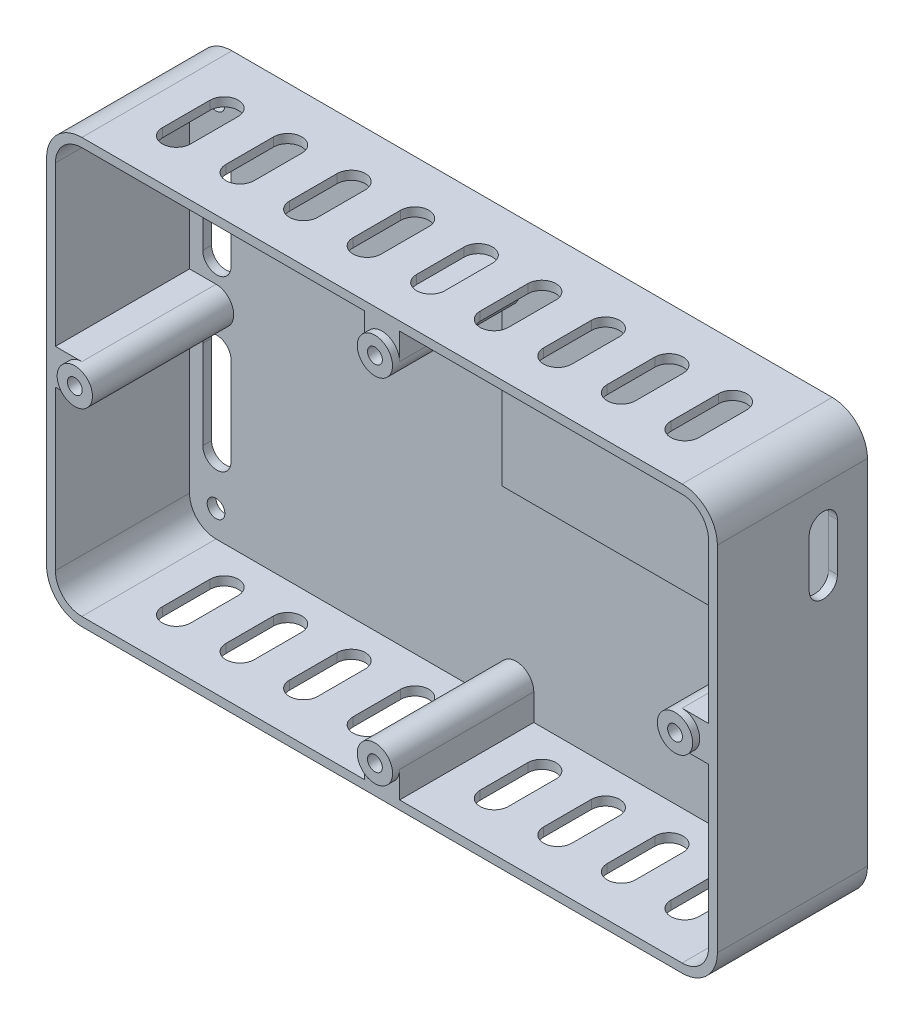
SolidWorks part; units mm, degrees
ref_plane "Front Plane" through (0, 0, 0) normal (0, 0, 1) x (1, 0, 0)
ref_plane "Top Plane" through (0, 0, 0) normal (0, 1, 0) x (1, 0, 0)
ref_plane "Right Plane" through (0, 0, 0) normal (1, 0, 0) x (0, 0, -1)
sketch "Sketch1" plane through (0, 0, 0) normal (0, 0, 1) x (1, 0, 0)
  line L0 (92.3241, -194.8914) -> (92.3241, -94.8914) construction
  line L1 (-85.1759, -202.3914) -> (84.8241, -202.3914) construction
  line L2 (84.8241, -87.3914) -> (-85.1759, -87.3914) construction
  line L3 (-92.6759, -94.8914) -> (-92.6759, -194.8914) construction
  line L4 (-85.1759, -204.8914) -> (84.8241, -204.8914)
  line L5 (94.8241, -194.8914) -> (94.8241, -94.8914)
  line L6 (84.8241, -84.8914) -> (-85.1759, -84.8914)
  line L7 (-95.1759, -94.8914) -> (-95.1759, -194.8914)
  line L8 (-85.1759, -204.8914) -> (84.8241, -204.8914)
  line L9 (94.8241, -194.8914) -> (94.8241, -94.8914)
  line L10 (84.8241, -84.8914) -> (-85.1759, -84.8914)
  line L11 (-95.1759, -94.8914) -> (-95.1759, -194.8914)
  line L12 (92.3241, -194.8914) -> (92.3241, -94.8914)
  line L13 (-85.1759, -202.3914) -> (84.8241, -202.3914)
  line L14 (84.8241, -87.3914) -> (-85.1759, -87.3914)
  line L15 (-92.6759, -94.8914) -> (-92.6759, -194.8914)
  line L16 (-85.1759, -87.3914) -> (-85.1759, -87.2984)
  circle A0 centre (-85.1759, -94.8914) radius 5.5
  circle A1 centre (84.8241, -94.8914) radius 5.9759
  circle A2 centre (84.8241, -194.8914) radius 5.9759
  circle A3 centre (-85.1759, -194.8914) radius 5.9759
  arc A4 (84.8241, -204.8914) -> (94.8241, -194.8914) centre (84.8241, -194.8914) ccw
  arc A5 (94.8241, -94.8914) -> (84.8241, -84.8914) centre (84.8241, -94.8914) ccw
  arc A6 (-85.1759, -84.8914) -> (-95.1759, -94.8914) centre (-85.1759, -94.8914) ccw
  arc A7 (-95.1759, -194.8914) -> (-85.1759, -204.8914) centre (-85.1759, -194.8914) ccw
  arc A8 (84.8241, -204.8914) -> (94.8241, -194.8914) centre (84.8241, -194.8914) ccw
  arc A9 (94.8241, -94.8914) -> (84.8241, -84.8914) centre (84.8241, -94.8914) ccw
  arc A10 (-85.1759, -84.8914) -> (-95.1759, -94.8914) centre (-85.1759, -94.8914) ccw
  arc A11 (-95.1759, -194.8914) -> (-85.1759, -204.8914) centre (-85.1759, -194.8914) ccw
  circle A13 centre (-85.1759, -194.8914) radius 7.5
  circle A14 centre (84.8241, -94.8914) radius 7.5
  circle A15 centre (84.8241, -194.8914) radius 7.5
  arc A16 (-92.6759, -94.8914) -> (-85.1759, -87.3914) centre (-85.1759, -94.8914) ccw
  dimension "D2" = 11
  dimension "D1" = 0
extrude "Boss-Extrude1" add sketch "Sketch1" along normal blind 2
sketch "Sketch2" plane through (0, 0, 2) normal (0, 0, 1) x (1, 0, 0)
  line L4 (-95.1759, -94.8914) -> (-95.1759, -194.8914)
  line L5 (-85.1759, -204.8914) -> (84.8241, -204.8914)
  line L6 (94.8241, -194.8914) -> (94.8241, -94.8914)
  line L7 (84.8241, -84.8914) -> (-85.1759, -84.8914)
  line L8 (-95.1759, -94.8914) -> (-95.1759, -194.8914)
  line L9 (-85.1759, -204.8914) -> (84.8241, -204.8914)
  line L10 (94.8241, -194.8914) -> (94.8241, -94.8914)
  line L11 (84.8241, -84.8914) -> (-85.1759, -84.8914)
  arc A4 (-95.1759, -194.8914) -> (-85.1759, -204.8914) centre (-85.1759, -194.8914) ccw
  arc A5 (84.8241, -204.8914) -> (94.8241, -194.8914) centre (84.8241, -194.8914) ccw
  arc A6 (94.8241, -94.8914) -> (84.8241, -84.8914) centre (84.8241, -94.8914) ccw
  arc A7 (-85.1759, -84.8914) -> (-95.1759, -94.8914) centre (-85.1759, -94.8914) ccw
  arc A8 (-95.1759, -194.8914) -> (-85.1759, -204.8914) centre (-85.1759, -194.8914) ccw
  arc A9 (84.8241, -204.8914) -> (94.8241, -194.8914) centre (84.8241, -194.8914) ccw
  arc A10 (94.8241, -94.8914) -> (84.8241, -84.8914) centre (84.8241, -94.8914) ccw
  arc A11 (-85.1759, -84.8914) -> (-95.1759, -94.8914) centre (-85.1759, -94.8914) ccw
  dimension "D1" = 0
extrude "Boss-Extrude2" add sketch "Sketch2" along normal blind 2.5
sketch "Sketch3" plane through (0, 0, 4.5) normal (0, 0, 1) x (1, 0, 0)
  line L0 (-85.1759, -94.8914) -> (84.8241, -94.8914) construction
  line L1 (84.8241, -94.8914) -> (84.8241, -194.8914) construction
  line L2 (84.8241, -194.8914) -> (-85.1759, -194.8914) construction
  line L3 (-85.1759, -194.8914) -> (-85.1759, -94.8914) construction
  line L8 (-85.1759, -204.8914) -> (84.8241, -204.8914) construction
  line L9 (94.8241, -194.8914) -> (94.8241, -94.8914) construction
  line L10 (84.8241, -84.8914) -> (-85.1759, -84.8914) construction
  line L11 (-95.1759, -94.8914) -> (-95.1759, -194.8914) construction
  line L12 (-92.6759, -94.8914) -> (-92.6759, -194.8914)
  line L13 (-85.1759, -202.3914) -> (84.8241, -202.3914)
  line L14 (92.3241, -194.8914) -> (92.3241, -94.8914)
  line L15 (84.8241, -87.3914) -> (-85.1759, -87.3914)
  line L16 (-92.6759, -94.8914) -> (-92.6759, -194.8914)
  line L17 (-85.1759, -202.3914) -> (84.8241, -202.3914)
  line L18 (92.3241, -194.8914) -> (92.3241, -94.8914)
  line L19 (84.8241, -87.3914) -> (-85.1759, -87.3914)
  line L20 (-85.1759, -204.8914) -> (84.8241, -204.8914)
  line L21 (94.8241, -194.8914) -> (94.8241, -94.8914)
  line L22 (84.8241, -84.8914) -> (-85.1759, -84.8914)
  line L23 (-95.1759, -94.8914) -> (-95.1759, -194.8914)
  line L24 (-85.1759, -139.8914) -> (-92.6759, -139.8914)
  line L25 (-85.1759, -149.8914) -> (-92.6759, -149.8914)
  line L26 (-5.1759, -94.8914) -> (-5.1759, -87.3914)
  line L27 (4.8241, -94.8914) -> (4.8241, -87.3914)
  line L28 (-5.1759, -194.8914) -> (-5.1759, -202.3914)
  line L29 (4.8241, -194.8914) -> (4.8241, -202.3914)
  line L30 (84.8241, -139.8914) -> (92.3241, -139.8914)
  line L33 (84.8241, -149.8914) -> (92.3241, -149.8914)
  circle A0 centre (-0.1759, -94.8914) radius 5
  circle A1 centre (-85.1759, -144.8914) radius 5
  circle A2 centre (-0.1759, -194.8914) radius 5
  circle A3 centre (84.8241, -144.8914) radius 5
  arc A8 (-95.1759, -194.8914) -> (-85.1759, -204.8914) centre (-85.1759, -194.8914) ccw construction
  arc A9 (84.8241, -204.8914) -> (94.8241, -194.8914) centre (84.8241, -194.8914) ccw construction
  arc A10 (94.8241, -94.8914) -> (84.8241, -84.8914) centre (84.8241, -94.8914) ccw construction
  arc A11 (-85.1759, -84.8914) -> (-95.1759, -94.8914) centre (-85.1759, -94.8914) ccw construction
  arc A12 (-85.1759, -87.3914) -> (-92.6759, -94.8914) centre (-85.1759, -94.8914) ccw
  arc A13 (-92.6759, -194.8914) -> (-85.1759, -202.3914) centre (-85.1759, -194.8914) ccw
  arc A14 (84.8241, -202.3914) -> (92.3241, -194.8914) centre (84.8241, -194.8914) ccw
  arc A15 (92.3241, -94.8914) -> (84.8241, -87.3914) centre (84.8241, -94.8914) ccw
  arc A16 (-85.1759, -87.3914) -> (-92.6759, -94.8914) centre (-85.1759, -94.8914) ccw
  arc A17 (-92.6759, -194.8914) -> (-85.1759, -202.3914) centre (-85.1759, -194.8914) ccw
  arc A18 (84.8241, -202.3914) -> (92.3241, -194.8914) centre (84.8241, -194.8914) ccw
  arc A19 (92.3241, -94.8914) -> (84.8241, -87.3914) centre (84.8241, -94.8914) ccw
  arc A20 (-95.1759, -194.8914) -> (-85.1759, -204.8914) centre (-85.1759, -194.8914) ccw
  arc A21 (84.8241, -204.8914) -> (94.8241, -194.8914) centre (84.8241, -194.8914) ccw
  arc A22 (94.8241, -94.8914) -> (84.8241, -84.8914) centre (84.8241, -94.8914) ccw
  arc A23 (-85.1759, -84.8914) -> (-95.1759, -94.8914) centre (-85.1759, -94.8914) ccw
  arc M9 (-85.1759, -84.8914) -> (-95.1759, -94.8914) centre (-85.1759, -94.8914) ccw
  line M10 (-95.1759, -94.8914) -> (-95.1759, -194.8914)
  arc M11 (-95.1759, -194.8914) -> (-85.1759, -204.8914) centre (-85.1759, -194.8914) ccw
  line M12 (-85.1759, -204.8914) -> (84.8241, -204.8914)
  arc M13 (84.8241, -204.8914) -> (94.8241, -194.8914) centre (84.8241, -194.8914) ccw
  line M14 (94.8241, -194.8914) -> (94.8241, -94.8914)
  arc M15 (94.8241, -94.8914) -> (84.8241, -84.8914) centre (84.8241, -94.8914) ccw
  line M16 (84.8241, -84.8914) -> (-85.1759, -84.8914)
  dimension "D1" = 10
  dimension "D2" = 2.5
extrude "Boss-Extrude3" add sketch "Sketch3" along normal blind 38 contours A19 L18 A18 L17 A17 L16 A16 L19 M16 M9 M10 M11 M12 M13 M14 M15 | A0 L27 L19 L26 | A0 | A3 | A3 L33 L18 L30 | A2 | A2 L28 L17 L29 | A1 L24 L16 L25 | A1
sketch "Sketch5" plane through (0, 0, 42.5) normal (0, 0, 1) x (1, 0, 0)
  circle A0 centre (-85.1759, -144.8914) radius 5
  circle A1 centre (-0.1759, -94.8914) radius 5
  circle A2 centre (84.8241, -144.8914) radius 5
  circle A3 centre (-0.1759, -194.8914) radius 5
extrude "Boss-Extrude4" add sketch "Sketch5" along normal blind 2
sketch "Sketch6" plane through (0, 0, 4.5) normal (0, 0, 1) x (1, 0, 0)
  line L2 (-80.9375, -181.3615) -> (-80.9375, -156.298)
  line L3 (-88.9375, -156.298) -> (-88.9375, -181.3615)
  line L4 (-80.9375, -181.3615) -> (-80.9375, -156.298)
  line L5 (-88.9375, -156.298) -> (-88.9375, -181.3615)
  line L6 (-80.9375, -133.4848) -> (-80.9375, -108.4213)
  line L7 (-88.9375, -108.4213) -> (-88.9375, -133.4848)
  line L8 (-80.9375, -133.4848) -> (-80.9375, -108.4213)
  line L9 (-88.9375, -108.4213) -> (-88.9375, -133.4848)
  arc A2 (-80.9375, -156.298) -> (-88.9375, -156.298) centre (-84.9375, -156.298) ccw
  arc A3 (-88.9375, -181.3615) -> (-80.9375, -181.3615) centre (-84.9375, -181.3615) ccw
  arc A4 (-80.9375, -156.298) -> (-88.9375, -156.298) centre (-84.9375, -156.298) ccw
  arc A5 (-88.9375, -181.3615) -> (-80.9375, -181.3615) centre (-84.9375, -181.3615) ccw
  arc A6 (-88.9375, -133.4848) -> (-80.9375, -133.4848) centre (-84.9375, -133.4848) ccw
  arc A7 (-80.9375, -108.4213) -> (-88.9375, -108.4213) centre (-84.9375, -108.4213) ccw
  arc A8 (-88.9375, -133.4848) -> (-80.9375, -133.4848) centre (-84.9375, -133.4848) ccw
  arc A9 (-80.9375, -108.4213) -> (-88.9375, -108.4213) centre (-84.9375, -108.4213) ccw
  dimension "D1" = 0
  dimension "D2" = 0
extrude "Cut-Extrude1" cut sketch "Sketch6" against normal blind 5
hole_wizard "Tap Drill for M5 Tap2" positions "Sketch12" profile "Sketch11" hole size "M5" standard "ISO"
sketch "Sketch12" plane through (0, 0, 44.5) normal (0, 0, 1) x (1, 0, 0)
  point P0 (-0.1759, -94.8914)
  point P3 (-85.1759, -144.8914)
  point P6 (84.8241, -144.8914)
  point P9 (-0.1759, -194.8914)
sketch "Sketch11" plane through (-0.1759, -94.8914, 44.5) normal (1, 0, 0) x (0, -1, 0)
  line L0 (0, 0) -> (0, 21.2618)
  line L1 (0, 21.2618) -> (2.1, 20)
  line L2 (2.1, 20) -> (2.1, 0)
  line L5 (2.1, 0) -> (0, 0)
  line L10 (0, 21.2618) -> (-2.1, 20) construction
  line L11 (0, -6.35) -> (0, 107.95) construction
  dimension "Hole Dia." = 4.2
  dimension "Hole Depth" = 20
  dimension "Drill Angle" = 118
hole_wizard "Ø5.0 (5) Diameter Hole1" positions "Sketch13" profile "Sketch14" hole size "Ø5.0" standard "ISO"
sketch "Sketch13" plane through (0, 0, 4.5) normal (0, 0, 1) x (1, 0, 0)
  point P0 (-85.1759, -94.8914)
  point P3 (-85.1759, -94.8914)
  point P6 (-85.1759, -194.8914)
  point P9 (84.8241, -194.8914)
  point P12 (84.8241, -94.8914)
sketch "Sketch14" plane through (-85.1759, -94.8914, 4.5) normal (1, 0, 0) x (0, -1, 0)
  line L0 (0, 0) -> (0, 4.0022)
  line L1 (0, 4.0022) -> (2.5, 2.5)
  line L2 (2.5, 2.5) -> (2.5, 0)
  line L5 (2.5, 0) -> (0, 0)
  line L10 (0, 4.0022) -> (-2.5, 2.5) construction
  line L11 (0, -6.35) -> (0, 107.95) construction
  dimension "Hole Dia." = 5
  dimension "Hole Depth" = 2.5
  dimension "Drill Angle" = 118
sketch "Sketch20" plane through (0, -204.8914, 0) normal (0, -1, 0) x (1, 0, 0)
  line L4 (-85.1759, 42.5) -> (-85.1759, 0) construction
  dimension "D2" = 42.5
sketch "Sketch24" plane through (94.8241, -110.0673, 0) normal (-1, 0, 0) x (0, -1, 0)
  line L2 (-4.4259, 8.5) -> (9.0741, 8.5)
  line L3 (9.0741, 16.5) -> (-4.4259, 16.5)
  line L4 (-15.1759, 42.5) -> (-15.1759, 0) construction
  arc A2 (9.0741, 8.5) -> (9.0741, 16.5) centre (9.0741, 12.5) ccw
  arc A3 (-4.4259, 16.5) -> (-4.4259, 8.5) centre (-4.4259, 12.5) ccw
  dimension "D1" = 10.75
extrude "Cut-Extrude7" cut sketch "Sketch24" along normal blind 2.5
sketch "Sketch25" plane through (0, 0, 4.5) normal (0, 0, 1) x (1, 0, 0)
  line L1 (-0.1759, -87.3914) -> (84.8241, -87.3914)
  line L2 (-0.1759, -87.3914) -> (-0.1759, -144.8914)
  line L3 (-0.1759, -144.8914) -> (92.3241, -144.8914)
  line L4 (92.3241, -94.8914) -> (92.3241, -144.8914)
  circle A0 centre (84.8241, -94.8914) radius 7.5
  line M19 (84.8241, -87.3914) -> (4.8241, -87.3914)
  line M20 (4.8241, -87.3914) -> (4.8241, -94.8914)
  arc M21 (4.8241, -94.8914) -> (-5.1759, -94.8914) centre (-0.1759, -94.8914) cw
  arc M39 (84.8241, -149.8914) -> (84.8241, -139.8914) centre (84.8241, -144.8914) cw
  line M40 (84.8241, -139.8914) -> (92.3241, -139.8914)
  line M41 (92.3241, -139.8914) -> (92.3241, -94.8914)
extrude "Boss-Extrude5" add sketch "Sketch25" along normal up to surface (4 mm away) separate body contours A0 L2 L3 M19 M20 M21 M39 M40 M41 up to face at (93.5741, -112.3914, 8.5)
sketch "Sketch31" plane through (0, -204.8914, 0) normal (0, -1, 0) x (1, 0, 0)
  line L0 (-72.1759, 28.704) -> (-72.1759, 15.204) construction
  line L1 (-68.1759, 28.704) -> (-68.1759, 15.204)
  line L2 (-76.1759, 28.704) -> (-76.1759, 15.204)
  line L3 (-85.1759, 42.5) -> (-85.1759, 0) construction
  line L4 (-54.1759, 28.704) -> (-54.1759, 15.204) construction
  line L5 (-50.1759, 28.704) -> (-50.1759, 15.204)
  line L6 (-58.1759, 28.704) -> (-58.1759, 15.204)
  line L7 (-36.1759, 28.704) -> (-36.1759, 15.204) construction
  line L8 (-32.1759, 28.704) -> (-32.1759, 15.204)
  line L9 (-40.1759, 28.704) -> (-40.1759, 15.204)
  line L10 (-18.1759, 28.704) -> (-18.1759, 15.204) construction
  line L11 (-14.1759, 28.704) -> (-14.1759, 15.204)
  line L12 (-22.1759, 28.704) -> (-22.1759, 15.204)
  line L13 (-0.1759, 28.704) -> (-0.1759, 15.204) construction
  line L14 (3.8241, 28.704) -> (3.8241, 15.204)
  line L15 (-4.1759, 28.704) -> (-4.1759, 15.204)
  line L16 (17.8241, 28.704) -> (17.8241, 15.204) construction
  line L17 (21.8241, 28.704) -> (21.8241, 15.204)
  line L18 (13.8241, 28.704) -> (13.8241, 15.204)
  line L19 (35.8241, 28.704) -> (35.8241, 15.204) construction
  line L20 (39.8241, 28.704) -> (39.8241, 15.204)
  line L21 (31.8241, 28.704) -> (31.8241, 15.204)
  line L22 (53.8241, 28.704) -> (53.8241, 15.204) construction
  line L23 (57.8241, 28.704) -> (57.8241, 15.204)
  line L24 (49.8241, 28.704) -> (49.8241, 15.204)
  line L25 (71.8241, 28.704) -> (71.8241, 15.204) construction
  line L26 (75.8241, 28.704) -> (75.8241, 15.204)
  line L27 (67.8241, 28.704) -> (67.8241, 15.204)
  arc A0 (-68.1759, 28.704) -> (-76.1759, 28.704) centre (-72.1759, 28.704) ccw
  arc A1 (-76.1759, 15.204) -> (-68.1759, 15.204) centre (-72.1759, 15.204) ccw
  arc A2 (-50.1759, 28.704) -> (-58.1759, 28.704) centre (-54.1759, 28.704) ccw
  arc A3 (-58.1759, 15.204) -> (-50.1759, 15.204) centre (-54.1759, 15.204) ccw
  arc A4 (-32.1759, 28.704) -> (-40.1759, 28.704) centre (-36.1759, 28.704) ccw
  arc A5 (-40.1759, 15.204) -> (-32.1759, 15.204) centre (-36.1759, 15.204) ccw
  arc A6 (-14.1759, 28.704) -> (-22.1759, 28.704) centre (-18.1759, 28.704) ccw
  arc A7 (-22.1759, 15.204) -> (-14.1759, 15.204) centre (-18.1759, 15.204) ccw
  arc A8 (3.8241, 28.704) -> (-4.1759, 28.704) centre (-0.1759, 28.704) ccw
  arc A9 (-4.1759, 15.204) -> (3.8241, 15.204) centre (-0.1759, 15.204) ccw
  arc A10 (21.8241, 28.704) -> (13.8241, 28.704) centre (17.8241, 28.704) ccw
  arc A11 (13.8241, 15.204) -> (21.8241, 15.204) centre (17.8241, 15.204) ccw
  arc A12 (39.8241, 28.704) -> (31.8241, 28.704) centre (35.8241, 28.704) ccw
  arc A13 (31.8241, 15.204) -> (39.8241, 15.204) centre (35.8241, 15.204) ccw
  arc A14 (57.8241, 28.704) -> (49.8241, 28.704) centre (53.8241, 28.704) ccw
  arc A15 (49.8241, 15.204) -> (57.8241, 15.204) centre (53.8241, 15.204) ccw
  arc A16 (75.8241, 28.704) -> (67.8241, 28.704) centre (71.8241, 28.704) ccw
  arc A17 (67.8241, 15.204) -> (75.8241, 15.204) centre (71.8241, 15.204) ccw
  point P2 (-72.1759, 21.954)
  point P9 (-76.1759, 21.954)
  point P14 (-54.1759, 21.954)
  point P21 (-36.1759, 21.954)
  point P28 (-18.1759, 21.954)
  point P35 (-0.1759, 21.954)
  point P42 (17.8241, 21.954)
  point P49 (35.8241, 21.954)
  point P56 (53.8241, 21.954)
  point P63 (71.8241, 21.954)
  dimension "D1" = 9
  dimension "D2" = 8
  dimension "D3" = 13.5
  dimension "D4" = 9
extrude "Cut-Extrude8" cut sketch "Sketch31" against normal blind 2.5
sketch "Sketch32" plane through (0, -84.8914, 0) normal (0, 1, 0) x (1, 0, 0)
  line L0 (67.8241, -28.704) -> (67.8241, -15.204) construction
  line L1 (75.8241, -15.204) -> (75.8241, -28.704) construction
  line L2 (67.8241, -28.704) -> (67.8241, -15.204)
  line L3 (75.8241, -15.204) -> (75.8241, -28.704)
  line L4 (49.8241, -28.704) -> (49.8241, -15.204)
  line L5 (57.8241, -15.204) -> (57.8241, -28.704)
  line L6 (31.8241, -28.704) -> (31.8241, -15.204)
  line L7 (39.8241, -15.204) -> (39.8241, -28.704)
  line L8 (13.8241, -28.704) -> (13.8241, -15.204)
  line L9 (21.8241, -15.204) -> (21.8241, -28.704)
  line L10 (-4.1759, -28.704) -> (-4.1759, -15.204)
  line L11 (3.8241, -15.204) -> (3.8241, -28.704)
  line L12 (-22.1759, -28.704) -> (-22.1759, -15.204)
  line L13 (-14.1759, -15.204) -> (-14.1759, -28.704)
  line L14 (-40.1759, -28.704) -> (-40.1759, -15.204)
  line L15 (-32.1759, -15.204) -> (-32.1759, -28.704)
  line L16 (-58.1759, -28.704) -> (-58.1759, -15.204)
  line L17 (-50.1759, -15.204) -> (-50.1759, -28.704)
  line L18 (-76.1759, -28.704) -> (-76.1759, -15.204)
  line L19 (-68.1759, -15.204) -> (-68.1759, -28.704)
  arc A0 (75.8241, -15.204) -> (67.8241, -15.204) centre (71.8241, -15.204) ccw construction
  arc A1 (67.8241, -28.704) -> (75.8241, -28.704) centre (71.8241, -28.704) ccw construction
  arc A2 (75.8241, -15.204) -> (67.8241, -15.204) centre (71.8241, -15.204) ccw
  arc A3 (67.8241, -28.704) -> (75.8241, -28.704) centre (71.8241, -28.704) ccw
  arc A4 (57.8241, -15.204) -> (49.8241, -15.204) centre (53.8241, -15.204) ccw
  arc A5 (49.8241, -28.704) -> (57.8241, -28.704) centre (53.8241, -28.704) ccw
  arc A6 (39.8241, -15.204) -> (31.8241, -15.204) centre (35.8241, -15.204) ccw
  arc A7 (31.8241, -28.704) -> (39.8241, -28.704) centre (35.8241, -28.704) ccw
  arc A8 (21.8241, -15.204) -> (13.8241, -15.204) centre (17.8241, -15.204) ccw
  arc A9 (13.8241, -28.704) -> (21.8241, -28.704) centre (17.8241, -28.704) ccw
  arc A10 (3.8241, -15.204) -> (-4.1759, -15.204) centre (-0.1759, -15.204) ccw
  arc A11 (-4.1759, -28.704) -> (3.8241, -28.704) centre (-0.1759, -28.704) ccw
  arc A12 (-14.1759, -15.204) -> (-22.1759, -15.204) centre (-18.1759, -15.204) ccw
  arc A13 (-22.1759, -28.704) -> (-14.1759, -28.704) centre (-18.1759, -28.704) ccw
  arc A14 (-32.1759, -15.204) -> (-40.1759, -15.204) centre (-36.1759, -15.204) ccw
  arc A15 (-40.1759, -28.704) -> (-32.1759, -28.704) centre (-36.1759, -28.704) ccw
  arc A16 (-50.1759, -15.204) -> (-58.1759, -15.204) centre (-54.1759, -15.204) ccw
  arc A17 (-58.1759, -28.704) -> (-50.1759, -28.704) centre (-54.1759, -28.704) ccw
  arc A18 (-68.1759, -15.204) -> (-76.1759, -15.204) centre (-72.1759, -15.204) ccw
  arc A19 (-76.1759, -28.704) -> (-68.1759, -28.704) centre (-72.1759, -28.704) ccw
  dimension "D1" = 9
extrude "Cut-Extrude9" cut sketch "Sketch32" against normal blind 2.5
